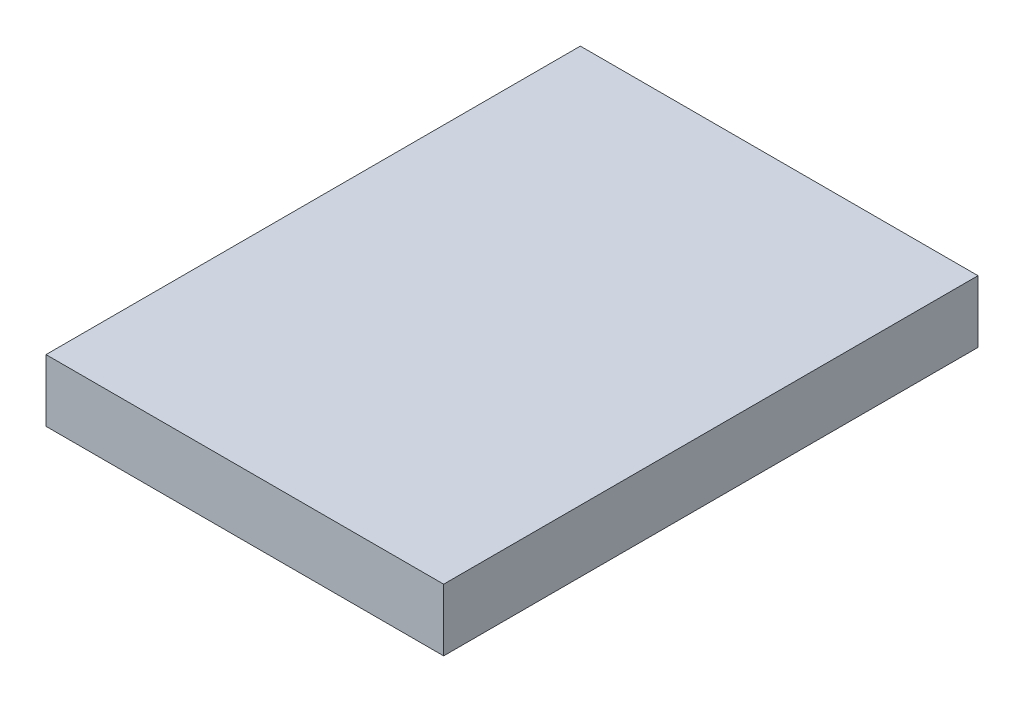
SolidWorks part; units mm, degrees
ref_plane "Front Plane" through (0, 0, 0) normal (0, 0, 1) x (1, 0, 0)
ref_plane "Top Plane" through (0, 0, 0) normal (0, 1, 0) x (1, 0, 0)
ref_plane "Right Plane" through (0, 0, 0) normal (1, 0, 0) x (0, 0, -1)
sketch "Sketch1" plane through (0, 0, 0) normal (0, 1, 0) x (1, 0, 0)
  line L1 (0, 0) -> (50.8, 0)
  line L2 (0, 0) -> (0, 68.2625)
  line L3 (0, 68.2625) -> (50.8, 68.2625)
  line L4 (50.8, 0) -> (50.8, 68.2625)
  dimension "D1" = 68.2625
  dimension "D2" = 50.8
extrude "Boss-Extrude1" add sketch "Sketch1" along normal blind 7.9375
